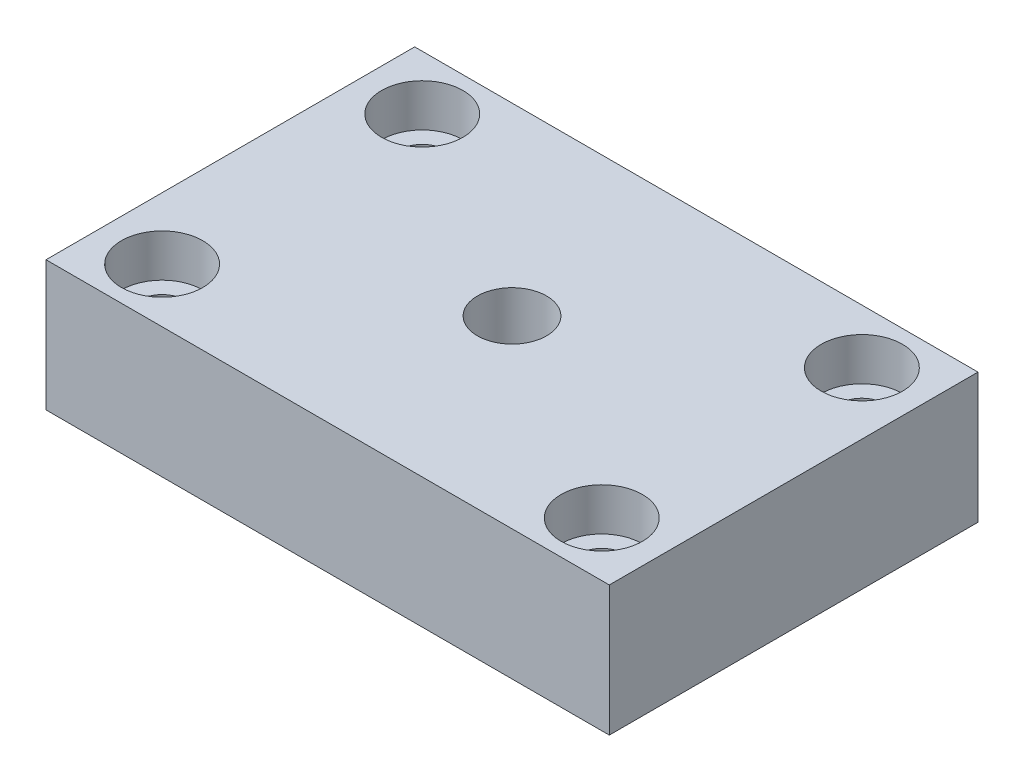
SolidWorks part; units mm, degrees
material "6061-T6 Al"
ref_plane "Front" through (0, 0, 0) normal (0, 0, 1) x (1, 0, 0)
ref_plane "Top" through (0, 0, 0) normal (0, 1, 0) x (1, 0, 0)
ref_plane "Right" through (0, 0, 0) normal (1, 0, 0) x (0, 0, -1)
sketch "Sketch1" plane through (0, 0, 0) normal (0, 1, 0) x (1, 0, 0)
  line L1 (-27.5, -18) -> (27.5, -18)
  line L2 (-27.5, -18) -> (-27.5, 18)
  line L3 (-27.5, 18) -> (27.5, 18)
  line L4 (27.5, -18) -> (27.5, 18)
  line L5 (-27.5, -18) -> (27.5, 18) construction
  line L6 (-27.5, 18) -> (27.5, -18) construction
  point P0 (0, 0)
  dimension "D1" = 55
  dimension "D2" = 36
extrude "Boss-Extrude1" add sketch "Sketch1" along normal blind 12.7
hole_wizard "CBORE for #8 Socket Head Cap Screw1" positions "Sketch3" profile "Sketch2" counterbore size "#8" standard "ANSI Inch" end condition through all
sketch "Sketch3" plane through (0, 12.7, 0) normal (0, 1, 0) x (-1, 0, 0)
  point P0 (21.463, -12.7)
  point P2 (21.463, 12.7)
  point P4 (-21.463, 12.7)
  point P6 (-21.463, -12.7)
  dimension "D1" = 12.7
  dimension "D2" = 12.7
  dimension "D3" = 21.463
  dimension "D4" = 21.463
sketch "Sketch2" plane through (-21.463, 12.7, -12.7) normal (1, 0, 0) x (0, 0, 1)
  line L0 (0, 0) -> (0, 12.7)
  line L1 (0, 12.7) -> (2.2479, 12.7)
  line L3 (2.2479, 12.7) -> (2.2479, 4.1656)
  line L4 (2.2479, 4.1656) -> (3.9687, 4.1656)
  line L5 (3.9687, 4.1656) -> (3.9687, 0)
  line L7 (3.9687, 0) -> (0, 0)
  line L11 (0, -6.35) -> (0, 107.95) construction
  dimension "Thru Hole Dia." = 4.4958
  dimension "Thru Hole Depth" = 12.7
  dimension "C'Bore Dia." = 7.9375
  dimension "C'Bore Depth" = 4.1656
hole_wizard "CBORE for 1/4 Socket Head Cap Screw1" positions "Sketch7" profile "Sketch6" counterbore size "1/4" standard "ANSI Inch" end condition through all
sketch "Sketch7" plane through (0, 0, 0) normal (0, -1, 0) x (-1, 0, 0)
  point P0 (0, 0)
sketch "Sketch6" plane through (0, 0, 0) normal (1, 0, 0) x (0, 0, -1)
  line L0 (0, 0) -> (0, 12.7)
  line L1 (0, 12.7) -> (3.3782, 12.7)
  line L3 (3.3782, 12.7) -> (3.3782, 6.35)
  line L4 (3.3782, 6.35) -> (5.5562, 6.35)
  line L5 (5.5562, 6.35) -> (5.5563, 0)
  line L7 (5.5563, 0) -> (0, 0)
  line L11 (0, -6.35) -> (0, 107.95) construction
  dimension "Thru Hole Dia." = 6.7564
  dimension "Thru Hole Depth" = 12.7
  dimension "C'Bore Dia." = 11.1125
  dimension "C'Bore Depth" = 6.35
